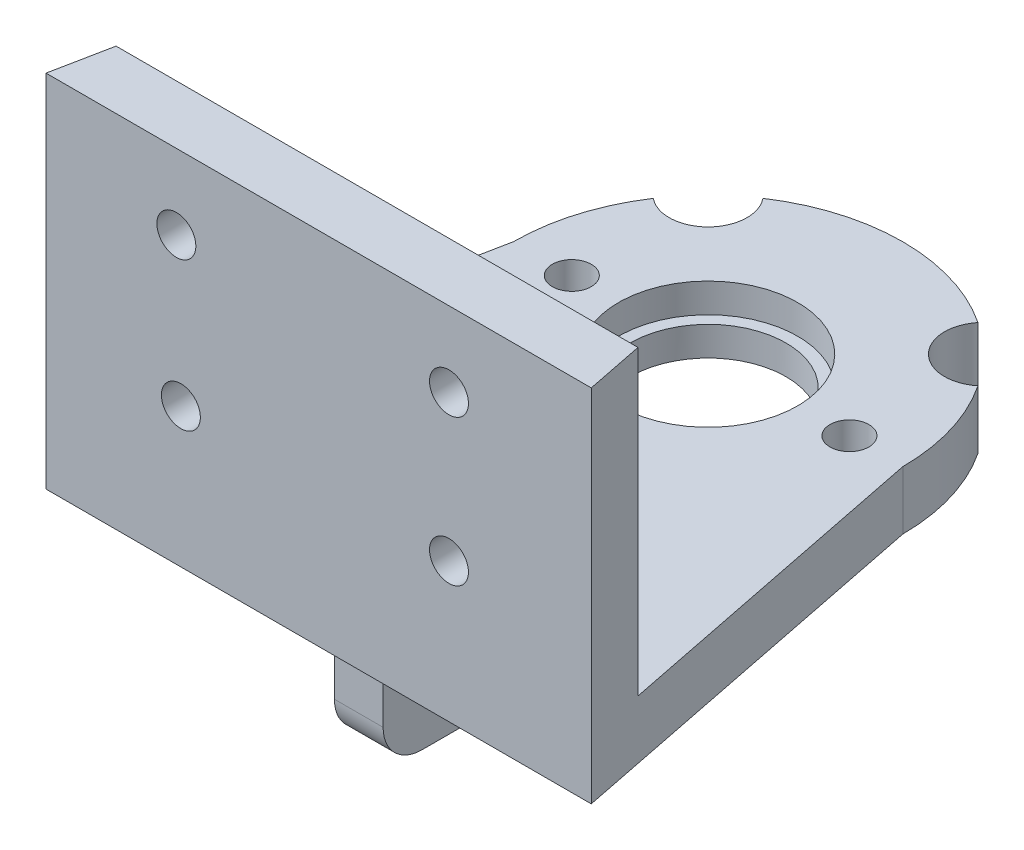
SolidWorks part; units mm, degrees
material "ABS"
ref_plane "Front Plane" through (0, 0, 0) normal (0, 0, 1) x (1, 0, 0)
ref_plane "Top Plane" through (0, 0, 0) normal (0, 1, 0) x (1, 0, 0)
ref_plane "Right Plane" through (0, 0, 0) normal (1, 0, 0) x (0, 0, -1)
other "Center of Mass"
sketch "Sketch1" plane through (0, 0, 0) normal (0, 1, 0) x (1, 0, 0)
  line L0 (-10, 0) -> (-14, -20)
  line L1 (10, 0) -> (14, -20)
  line L2 (0, 17.2103) -> (0, -39.4896) construction
  line L3 (-14, -20) -> (14, -20)
  arc A0 (-10, 0) -> (10, 0) centre (0, 0) cw
  dimension "D1" = 10
  dimension "D2" = 20
  dimension "D3" = 14
extrude "Boss-Extrude1" add sketch "Sketch1" along normal blind 3
sketch "Sketch2" plane through (0, 3, 0) normal (0, 1, 0) x (1, 0, 0)
  line L0 (-21.4034, 0) -> (30.5216, 0) construction
  circle A0 centre (0, 0) radius 4
  dimension "D1" = 8
extrude "Cut-Extrude1" cut sketch "Sketch2" against normal blind 13
sketch "Sketch3" plane through (0, 3, 0) normal (0, 1, 0) x (1, 0, 0)
  line L1 (-14, -20) -> (14, -20) construction
  line L2 (-10, 0) -> (0, 0) construction
  line L3 (-12.8, -14) -> (0, -14) construction
  line L4 (-10, 0) -> (-14, -20) construction
  line L5 (14, -20) -> (10, 0) construction
  point P3 (-6.4, -14)
  point P11 (-12.8, -14)
  point P12 (13.765, -18.8249)
  point P18 (0, -14)
  dimension "D1" = 6
sketch "Sketch4" plane through (0, 3, 0) normal (0, 1, 0) x (1, 0, 0)
  line L0 (0, 11.5358) -> (0, -14.2328) construction
  circle A0 centre (0, -7) radius 1
  circle A1 centre (-7, 0) radius 1
  circle A2 centre (0, 7) radius 1
  circle A3 centre (7, 0) radius 1
  point P0 (0, -7)
  point P15 (0, 0)
  dimension "D2" = 2
  dimension "D1" = 7
  dimension "D3" = 4
sketch "Sketch5" plane through (0, 3, 0) normal (0, 1, 0) x (1, 0, 0)
  line L0 (-13.4, -17) -> (13.4, -17)
  line L1 (-10, 0) -> (-14, -20) construction
  line L2 (14, -20) -> (10, 0) construction
  line L3 (-13.4, -17) -> (-14, -20)
  line L4 (-14, -20) -> (14, -20)
  line L5 (14, -20) -> (13.4, -17)
  dimension "D1" = 3
extrude "Boss-Extrude2" add sketch "Sketch5" along normal blind 15.5
sketch "Sketch6" plane through (0, 3, 0) normal (0, 1, 0) x (1, 0, 0)
  circle A0 centre (0, 0) radius 4.6
  dimension "D1" = 9.2
extrude "Cut-Extrude4" cut sketch "Sketch6" against normal blind 1.5
sketch "Sketch7" plane through (0, 3, 0) normal (0, 1, 0) x (1, 0, 0)
  line L0 (0, 12.0905) -> (0, -12.7025) construction
  line L1 (-13.0501, 13.0501) -> (0, 0) construction
  circle A0 centre (-7.0711, 7.0711) radius 2
  arc A1 (10, 0) -> (-10, 0) centre (0, 0) ccw construction
  circle A2 centre (7.0711, 7.0711) radius 2
  dimension "D1" = 4
extrude "Cut-Extrude5" cut sketch "Sketch7" against normal blind 10
sketch "Sketch8" plane through (0, 0, 17) normal (0, 0, -1) x (-1, 0, 0)
  line L0 (-13.4, 18.5) -> (13.4, 18.5) construction
  circle A0 centre (-6.6939, 7.1518) radius 1 construction
  circle A1 centre (-6.6939, 14.6518) radius 1 construction
  circle A2 centre (7.3061, 14.6518) radius 1 construction
  circle A3 centre (7.0737, 7.1518) radius 1 construction
  circle A4 centre (-6.6939, 7.1518) radius 1
  circle A5 centre (-6.6939, 14.6518) radius 1
  circle A6 centre (7.3061, 14.6518) radius 1
  circle A7 centre (7.0737, 7.1518) radius 1
  dimension "D1" = 3.8482
extrude "Cut-Extrude6" cut sketch "Sketch8" against normal blind 10
extrude "Cut-Extrude9" cut sketch "Sketch4" against normal blind 3 contours A1
sketch "Sketch11" plane through (0, 3, 0) normal (0, 1, 0) x (1, 0, 0)
  line L0 (0, 17.2103) -> (0, -39.4896) construction
  circle A0 centre (0, -7.5979) radius 1
  circle A1 centre (7.2562, 0) radius 1
  dimension "D1" = 2
  dimension "D2" = 2
extrude "Cut-Extrude11" cut sketch "Sketch11" against normal blind 3
sketch "Sketch12" plane through (0, 0, 0) normal (0, -1, 0) x (1, 0, 0)
  line L1 (1.25, 10.9393) -> (-1.25, 10.9393)
  line L2 (1.25, 10.9393) -> (1.25, 17.9393)
  line L3 (1.25, 17.9393) -> (-1.25, 17.9393)
  line L4 (-1.25, 10.9393) -> (-1.25, 17.9393)
  line L5 (1.25, 10.9393) -> (-1.25, 17.9393) construction
  line L6 (1.25, 17.9393) -> (-1.25, 10.9393) construction
  point P0 (0, 14.4393)
  dimension "D1" = 2.5
  dimension "D2" = 7
extrude "Boss-Extrude3" add sketch "Sketch12" along normal blind 6 contours L1 L4 L3 L2
sketch "Sketch13" plane through (-1.25, 0, 0) normal (-1, 0, 0) x (0, 0, 1)
  line L0 (10.9393, -6) -> (17.9393, -6) construction
  circle A0 centre (14.4094, -3) radius 1
  dimension "D2" = 2
  dimension "D1" = 3
extrude "Cut-Extrude12" cut sketch "Sketch13" against normal blind 6 contours A0
fillet "Fillet1" radius 2 4 edges at (0, 0, 17.9393) (0, 0, 10.9393) (0, -6, 17.9393) (0, -6, 10.9393)
